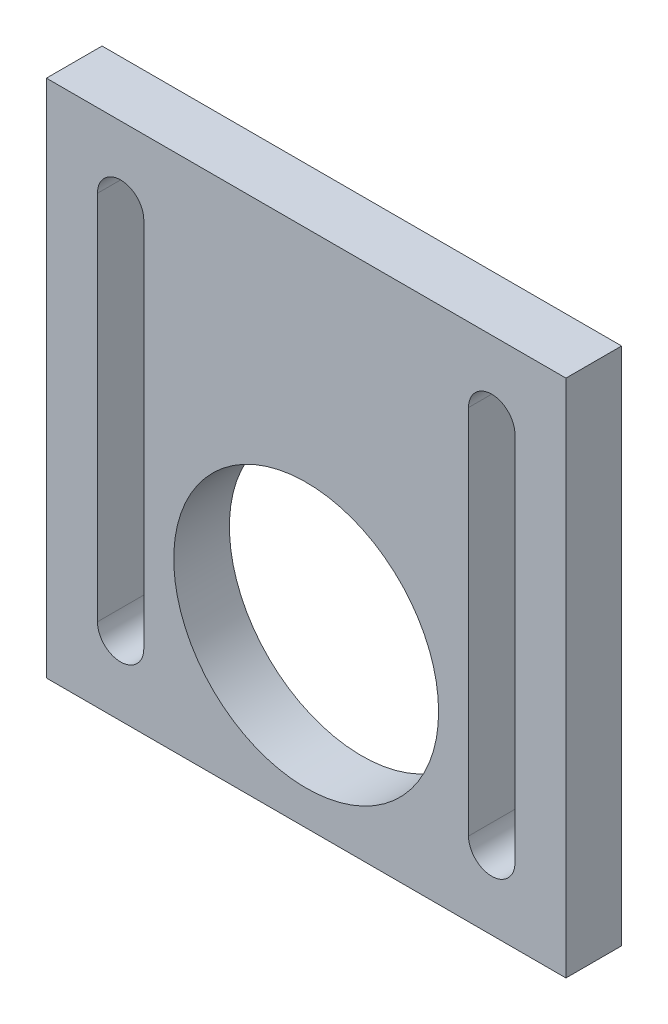
SolidWorks part; units mm, degrees
ref_plane "Front Plane" through (0, 0, 0) normal (0, 0, 1) x (1, 0, 0)
ref_plane "Top Plane" through (0, 0, 0) normal (0, 1, 0) x (1, 0, 0)
ref_plane "Right Plane" through (0, 0, 0) normal (1, 0, 0) x (0, 0, -1)
sketch "Sketch1" plane through (0, 0, 0) normal (0, 0, 1) x (1, 0, 0)
  line L1 (0, 0) -> (56, 0)
  line L2 (0, 0) -> (0, 56)
  line L3 (0, 56) -> (56, 56)
  line L4 (56, 0) -> (56, 56)
  dimension "D1" = 56
  dimension "D2" = 56
extrude "Boss-Extrude1" add sketch "Sketch1" along normal blind 6 contours L3 L4 L1 L2
sketch "Sketch2" plane through (0, 0, 6) normal (0, 0, 1) x (1, 0, 0)
  line L0 (28, 56) -> (28, 0) construction
  line L1 (0, 56) -> (56, 56) construction
  line L2 (0, 0) -> (56, 0) construction
  line L3 (0, 28) -> (56, 28) construction
  line L4 (0, 0) -> (0, 56) construction
  line L5 (56, 0) -> (56, 56) construction
  line L6 (8, 48) -> (8, 8) construction
  line L7 (10.5, 48) -> (10.5, 8)
  line L8 (5.5, 48) -> (5.5, 8)
  line L9 (48, 48) -> (48, 8) construction
  line L10 (50.5, 48) -> (50.5, 8)
  line L11 (45.5, 48) -> (45.5, 8)
  circle A0 centre (28, 18) radius 14.275
  arc A5 (10.5, 48) -> (5.5, 48) centre (8, 48) ccw
  arc A6 (5.5, 8) -> (10.5, 8) centre (8, 8) ccw
  arc A7 (50.5, 48) -> (45.5, 48) centre (48, 48) ccw
  arc A8 (45.5, 8) -> (50.5, 8) centre (48, 8) ccw
  point P15 (0, 0)
  point P17 (28, 17.9112)
  point P22 (8, 28)
  point P27 (48, 28)
  dimension "D1" = 28.55
  dimension "D2" = 18
  dimension "D6" = 8
  dimension "D7" = 8
  dimension "D8" = 8
  dimension "D9" = 8
  dimension "D10" = 8
  dimension "D11" = 8
  dimension "D12" = 8
  dimension "D13" = 8
  dimension "D14" = 5
  dimension "D15" = 5
extrude "Cut-Extrude1" cut sketch "Sketch2" against normal blind 6
